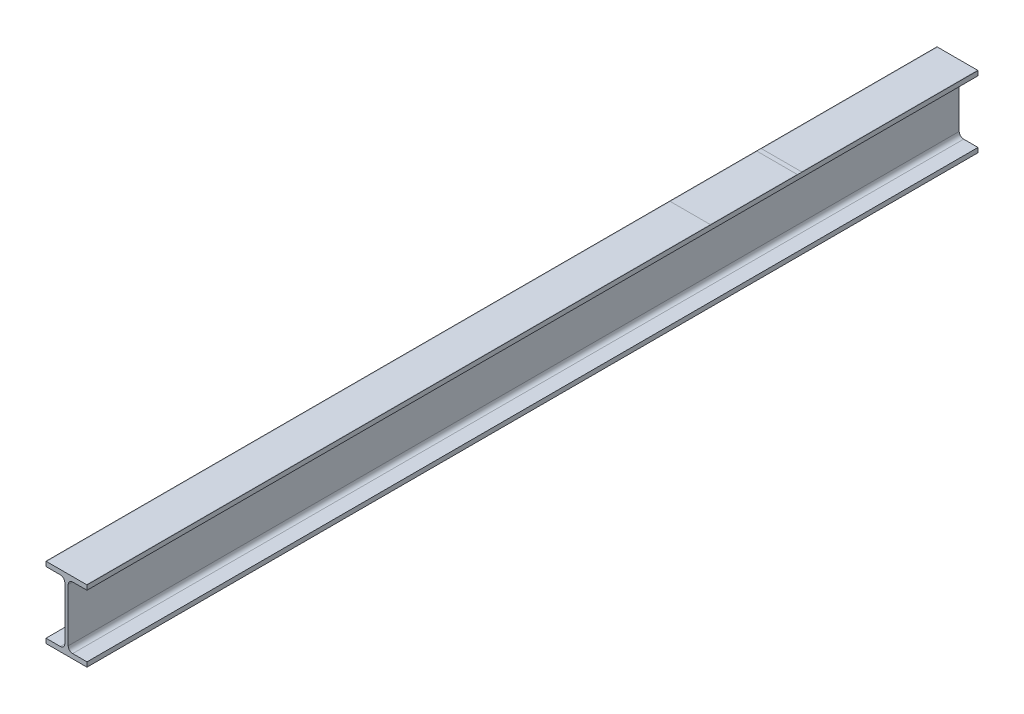
SolidWorks part; units mm, degrees
ref_plane "Ebene vorne" through (0, 0, 0) normal (0, 0, 1) x (1, 0, 0)
ref_plane "Ebene oben" through (0, 0, 0) normal (0, 1, 0) x (1, 0, 0)
ref_plane "Ebene rechts" through (0, 0, 0) normal (1, 0, 0) x (0, 0, -1)
sketch "Skizze1" plane through (0, 0, 0) normal (0, 0, 1) x (1, 0, 0)
  line L0 (0, 0) -> (0, 5.2)
  line L1 (0, 5.2) -> (16.1, 5.2)
  line L2 (21.1, 10.2) -> (21.1, 69.8)
  line L3 (16.1, 74.8) -> (0, 74.8)
  line L4 (0, 74.8) -> (0, 80)
  line L5 (0, 80) -> (46, 80)
  line L6 (46, 80) -> (46, 74.8)
  line L7 (46, 74.8) -> (29.9, 74.8)
  line L8 (24.9, 69.8) -> (24.9, 10.2)
  line L9 (29.9, 5.2) -> (46, 5.2)
  line L10 (46, 5.2) -> (46, 0)
  line L11 (46, 0) -> (0, 0)
  arc A0 (16.1, 5.2) -> (21.1, 10.2) centre (16.1, 10.2) ccw
  arc A1 (21.1, 69.8) -> (16.1, 74.8) centre (16.1, 69.8) ccw
  arc A2 (29.9, 74.8) -> (24.9, 69.8) centre (29.9, 69.8) ccw
  arc A3 (24.9, 10.2) -> (29.9, 5.2) centre (29.9, 10.2) ccw
extrude "Linear austragen1" add sketch "Skizze1" along normal blind 1000
ref_plane "Ebene1" through (0, 0, 500) normal (0, 0, 1) x (1, 0, 0)
ref_plane "Ebene2" through (0, 0, 300) normal (0, 0, 1) x (1, 0, 0)
ref_plane "Ebene3" through (0, 0, 200) normal (0, 0, 1) x (1, 0, 0)
ref_plane "Ebene Max Biegemoment" through (0, 0, 425) normal (0, 0, 1) x (1, 0, 0)
split "Abspalten1" [suppressed]
split "Abspalten2" [suppressed] bodies to split 107 108
split line "Trennlinie1"
sketch "Skizze2" plane through (0, 80, 0) normal (0, 1, 0) x (1, 0, 0)
  line L0 (0, -300) -> (0, 0) construction
  line L1 (0, -202.5) -> (46, -202.5)
  line L2 (0, -202.5) -> (0, -197.5)
  line L3 (0, -197.5) -> (46, -197.5)
  line L4 (46, -202.5) -> (46, -197.5)
  line L5 (46, -300) -> (46, 0) construction
  line L6 (0, -200) -> (46, -200) construction
  line L7 (-25.3, -200) -> (25.3, -200) construction
  dimension "D1" = 5
split line "Trennlinie2"
sketch "Skizze3" plane through (0, 80, 0) normal (0, 1, 0) x (1, 0, 0)
  line L0 (46, -1000) -> (0, -1000) construction
  line L1 (0.5, -1000) -> (45.5, -1000)
  line L2 (0.5, -1000) -> (0.5, 0)
  line L3 (0.5, 0) -> (45.5, 0)
  line L4 (45.5, -1000) -> (45.5, 0)
  line L5 (46, 0) -> (0, 0) construction
  line L6 (23, -1000) -> (23, 0) construction
  dimension "D1" = 45
split line "Trennlinie3"
